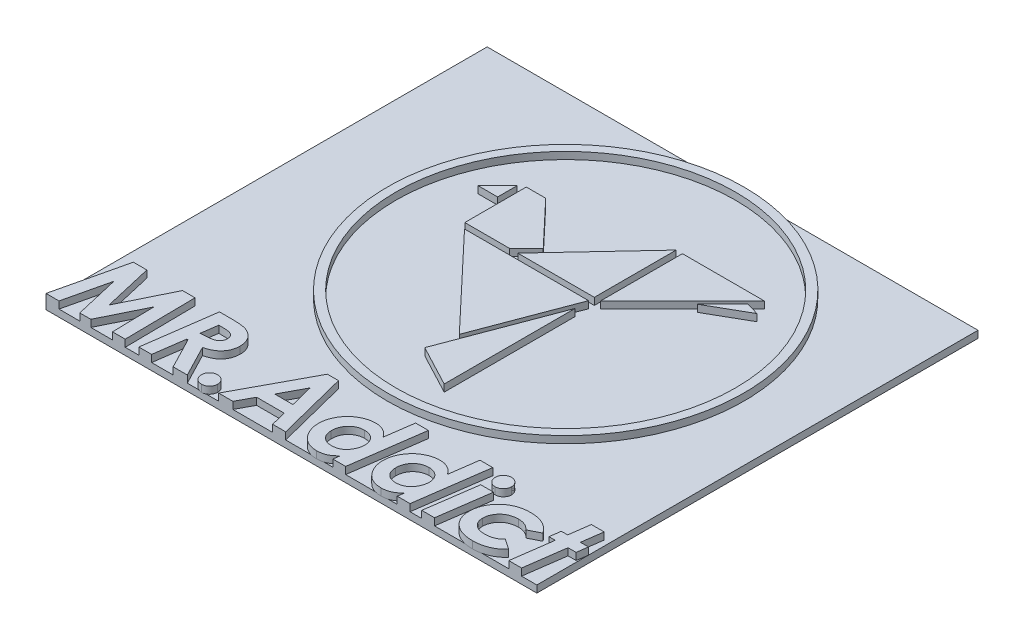
SolidWorks part; units mm, degrees
ref_plane "Front" through (0, 0, 0) normal (0, 0, 1) x (1, 0, 0)
ref_plane "Top" through (0, 0, 0) normal (0, 1, 0) x (1, 0, 0)
ref_plane "Right" through (0, 0, 0) normal (1, 0, 0) x (0, 0, -1)
sketch "Sketch1" plane through (0, 0, 0) normal (0, 1, 0) x (1, 0, 0)
  line L0 (69.0442, 256.0815) -> (402.3776, 256.0815) construction
  line L5 (68.034, 255.8843) -> (401.3674, 255.8843) construction
  line L6 (-10.0536, 18.5908) -> (-3.7888, 11.9574)
  line L7 (-3.7888, 11.9574) -> (-1.2828, 18.5908)
  line L8 (-1.2828, 18.5908) -> (-10.0536, 18.5908)
  line L9 (-10.4392, 18.9962) -> (-7.2897, 18.9962)
  line L10 (-7.2897, 18.9962) -> (-6.092, 20.1939)
  line L11 (-6.092, 20.1939) -> (-9.0666, 23.3434)
  line L12 (-9.0666, 23.3434) -> (-10.4392, 23.3434)
  line L13 (-10.4392, 23.3434) -> (-10.4392, 18.9962)
  line L14 (-12.2279, 21.7232) -> (-10.8459, 23.1052)
  line L15 (-10.8459, 23.1052) -> (-10.8459, 21.7232)
  line L16 (-10.8459, 21.7232) -> (-12.2279, 21.7232)
  line L17 (-6.6909, 18.9962) -> (-1.2828, 24.782)
  line L18 (-1.2828, 24.782) -> (-1.2828, 18.9962)
  line L19 (-1.2828, 18.9962) -> (-6.6909, 18.9962)
  line L20 (-0.8406, 24.782) -> (-0.8406, 18.9962)
  line L21 (-0.8406, 18.9962) -> (4.9452, 24.782)
  line L22 (4.9452, 24.782) -> (-0.8406, 24.782)
  line L23 (-1.2828, 17.6327) -> (-4.1957, 9.9221)
  line L24 (-4.1957, 9.9221) -> (-1.2828, 8.3828)
  line L25 (-1.2828, 8.3828) -> (-1.2828, 17.6327)
  line L26 (4.5766, 24.0081) -> (2.7893, 22.2207)
  line L27 (2.7893, 22.2207) -> (5.4611, 23.7501)
  line L28 (5.4611, 23.7501) -> (4.5766, 24.0081)
  circle A0 centre (-2.7434, 18.4326) radius 12
  circle A1 centre (-2.7434, 18.4326) radius 12.6084
extrude "Boss-Extrude3" add sketch "Sketch1" along normal blind 0.5 contours A1 A0 | L24 L25 L23 | L7 L8 L6 | L19 L18 L17 | L21 L22 L20 | L12 L13 L9 L10 L11 | L16 L15 L14 | L28 L26 L27
sketch "Sketch3" plane through (0, 0, 0) normal (0, 1, 0) x (1, 0, 0)
  text T0 "<b><i>MR.Addict</i></b>" font "Century Gothic" height 5
extrude "Boss-Extrude4" add sketch "Sketch3" along normal blind 0.5 separate body
sketch "Sketch4" plane through (0, 0, 0) normal (0, -1, 0) x (-1, 0, 0)
  line L1 (20.9029, -0.1463) -> (-13.7956, -0.1463)
  line L2 (20.9029, -0.1463) -> (20.9029, 31.041)
  line L3 (20.9029, 31.041) -> (-13.7956, 31.041)
  line L4 (-13.7956, -0.1463) -> (-13.7956, 31.041)
extrude "Boss-Extrude6" add sketch "Sketch4" along normal blind 0.5
